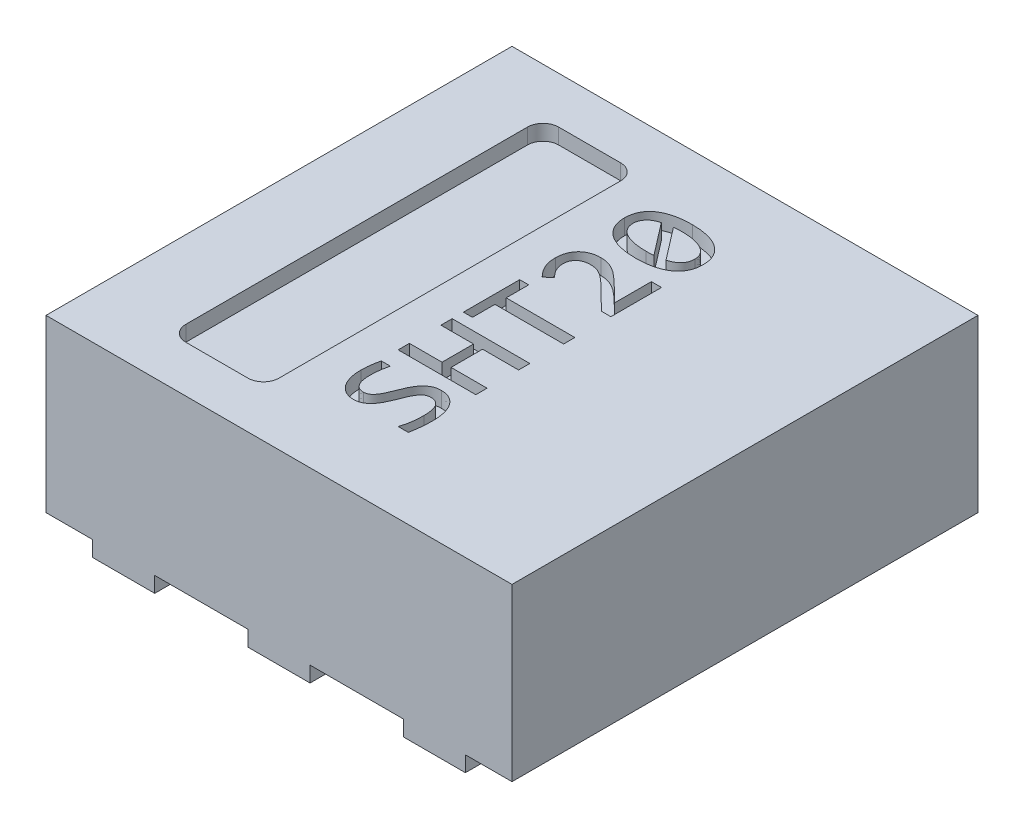
SolidWorks part; units mm, degrees
ref_plane "Спереди" through (0, 0, 0) normal (0, 0, 1) x (1, 0, 0)
ref_plane "Сверху" through (0, 0, 0) normal (0, 1, 0) x (1, 0, 0)
ref_plane "Справа" through (0, 0, 0) normal (1, 0, 0) x (0, 0, -1)
sketch "Эскиз1" plane through (0, 0, 0) normal (0, 1, 0) x (1, 0, 0)
  line L1 (-1.5, 1.5) -> (1.5, 1.5)
  line L2 (-1.5, 1.5) -> (-1.5, -1.5)
  line L3 (-1.5, -1.5) -> (1.5, -1.5)
  line L4 (1.5, 1.5) -> (1.5, -1.5)
  point P4 (-1.5, 0)
  point P6 (0, 1.5)
  dimension "D1" = 3
extrude "Бобышка-Вытянуть1" add sketch "Эскиз1" along normal blind 1.1
sketch "Эскиз2" plane through (0, 1.1, 0) normal (0, 1, 0) x (1, 0, 0)
  line L0 (1.5, -1.5) -> (1.5, 1.5) construction
  line L1 (-0.9, 1.2) -> (-0.5, 1.2)
  line L2 (-1, 1.1) -> (-1, -1.1)
  line L3 (-0.9, -1.2) -> (-0.5, -1.2)
  line L4 (-0.4, 1.1) -> (-0.4, -1.1)
  arc A0 (-0.5, -1.2) -> (-0.4, -1.1) centre (-0.5, -1.1) ccw
  arc A1 (-1, -1.1) -> (-0.9, -1.2) centre (-0.9, -1.1) ccw
  arc A2 (-0.5, 1.2) -> (-0.4, 1.1) centre (-0.5, 1.1) cw
  arc A3 (-0.9, 1.2) -> (-1, 1.1) centre (-0.9, 1.1) ccw
  point P4 (-0.7, -1.2)
  point P7 (-1, 0)
  point P13 (-1, -1.2)
  point P16 (-0.4, 1.2)
  point P19 (-1, 1.2)
  dimension "D4" = 0.1
  dimension "D1" = 2.4
  dimension "D2" = 0.6
  dimension "D3" = 2.2
extrude "Вырез-Вытянуть1" cut sketch "Эскиз2" against normal blind 0.1
sketch "Эскиз3" plane through (0, 0, 0) normal (0, -1, 0) x (1, 0, 0)
  line L0 (-1.5, 1.5) -> (1.5, 1.5) construction
  line L1 (1.2, -0.75) -> (-1.2, -0.75)
  line L2 (1.2, -0.75) -> (1.2, 0.75)
  line L3 (1.2, 0.75) -> (-0.8, 0.75)
  line L4 (-1.2, -0.75) -> (-1.2, 0.35)
  line L5 (1.2, -1.5) -> (0.8, -1.5)
  line L6 (1.2, -1.5) -> (1.2, -1.1)
  line L7 (1.2, -1.1) -> (0.8, -1.1)
  line L8 (0.8, -1.5) -> (0.8, -1.1)
  line L9 (0.2, -1.5) -> (-0.2, -1.5)
  line L10 (0.2, -1.5) -> (0.2, -1.1)
  line L11 (0.2, -1.1) -> (-0.2, -1.1)
  line L12 (-0.2, -1.5) -> (-0.2, -1.1)
  line L13 (-0.8, -1.5) -> (-1.2, -1.5)
  line L14 (-0.8, -1.5) -> (-0.8, -1.1)
  line L15 (-0.8, -1.1) -> (-1.2, -1.1)
  line L16 (-1.2, -1.5) -> (-1.2, -1.1)
  line L17 (1.2, 1.1) -> (0.8, 1.1)
  line L18 (1.2, 1.1) -> (1.2, 1.5)
  line L19 (1.2, 1.5) -> (0.8, 1.5)
  line L20 (0.8, 1.1) -> (0.8, 1.5)
  line L21 (0.2, 1.1) -> (-0.2, 1.1)
  line L22 (0.2, 1.1) -> (0.2, 1.5)
  line L23 (0.2, 1.5) -> (-0.2, 1.5)
  line L24 (-0.2, 1.1) -> (-0.2, 1.5)
  line L25 (1.5, -1.5) -> (-1.5, -1.5) construction
  line L26 (-0.8, 1.1) -> (-1.2, 1.1)
  line L27 (-0.8, 1.1) -> (-0.8, 1.5)
  line L28 (-0.8, 1.5) -> (-1.2, 1.5)
  line L29 (-1.2, 1.1) -> (-1.2, 1.5)
  line L30 (0, -1.5) -> (0, 1.5) construction
  line L31 (-1.2, 0.35) -> (-0.8, 0.75)
  point P1 (1.2, 0)
  point P30 (1, -1.5)
  point P33 (0, -1.5)
  point P34 (-1, -1.5)
  point P35 (1, 1.5)
  point P38 (0, -0.75)
  point P41 (0, 1.5)
  point P42 (0, 1.5)
  point P43 (-1, 1.5)
  point P44 (0, -1.5)
  dimension "D1" = 0.4
  dimension "D2" = 1
  dimension "D3" = 2.4
  dimension "D4" = 1.5
  dimension "D5" = 135
  dimension "D6" = 1.1
extrude "Бобышка-Вытянуть2" add sketch "Эскиз3" along normal blind 0.1
sketch "Эскиз4" plane through (0, 1.1, 0) normal (0, 1, 0) x (1, 0, 0)
  line L0 (0.3258, -1.0298) -> (0.3258, 0.9989) construction
  text T0 "SHT20" font "Consolas" height 0.5
  point P3 (0.3324, -1.0001)
  point P4 (0, 0)
  point P5 (0.3258, -1.0298)
extrude "Вырез-Вытянуть2" cut sketch "Эскиз4" against normal blind 0.1
